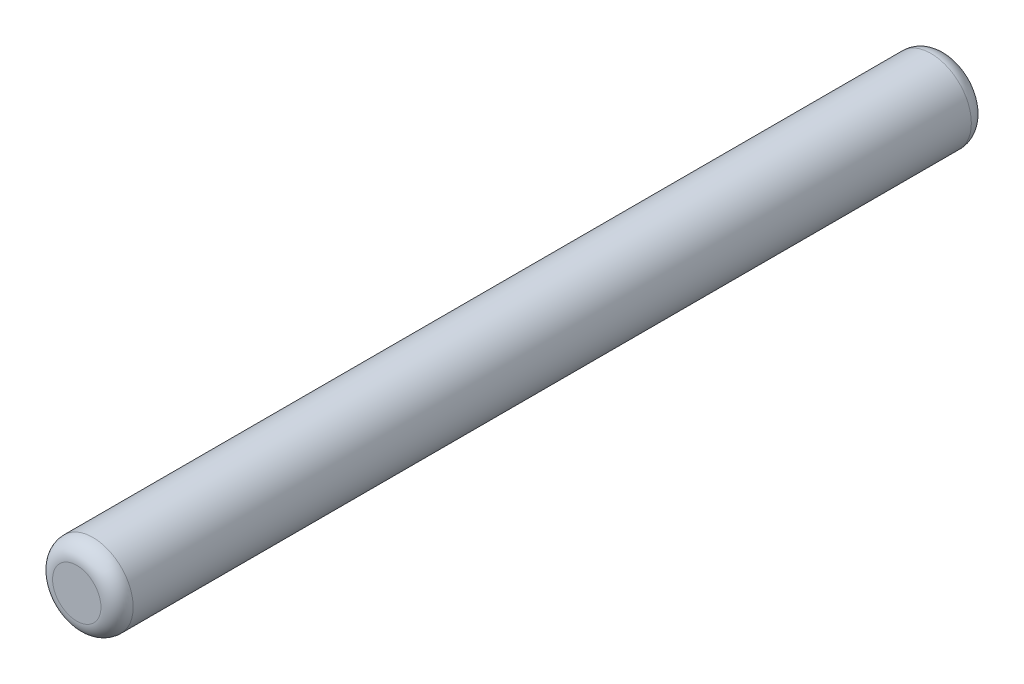
SolidWorks part; units mm, degrees
ref_plane "Front Plane" through (0, 0, 0) normal (0, 0, 1) x (1, 0, 0)
ref_plane "Top Plane" through (0, 0, 0) normal (0, 1, 0) x (1, 0, 0)
ref_plane "Right Plane" through (0, 0, 0) normal (1, 0, 0) x (0, 0, -1)
sketch "Sketch1" plane through (0, 0, 0) normal (0, 0, 1) x (1, 0, 0)
  circle A0 centre (0, 0) radius 2.5
  dimension "D1" = 5
extrude "Boss-Extrude1" add sketch "Sketch1" along normal blind 54
fillet "Fillet1" radius 1 2 edges at (2.5, 0, 0) (2.5, 0, 54)
